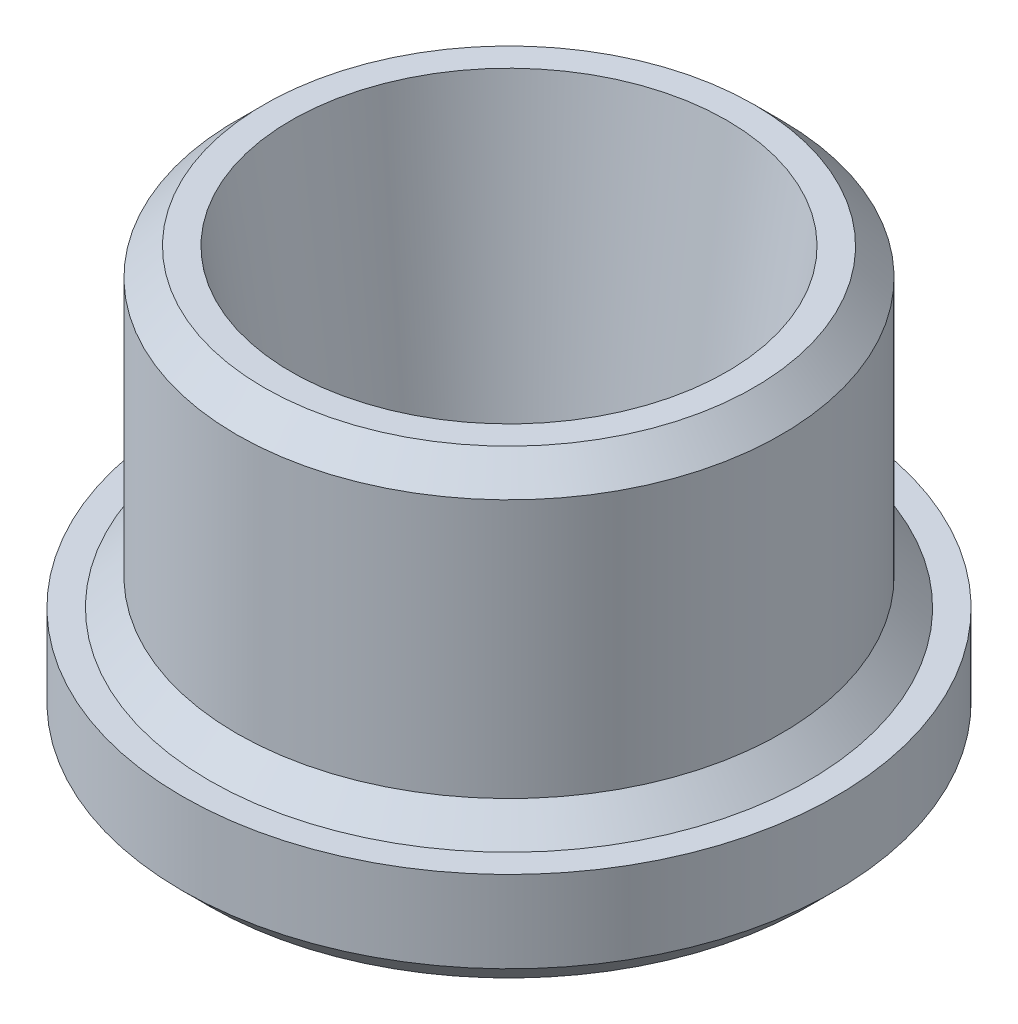
SolidWorks part; units mm, degrees
material "Alliage 1060"
ref_plane "Front Plane" through (0, 0, 0) normal (0, 0, 1) x (1, 0, 0)
ref_plane "Top Plane" through (0, 0, 0) normal (0, 1, 0) x (1, 0, 0)
ref_plane "Right Plane" through (0, 0, 0) normal (1, 0, 0) x (0, 0, -1)
sketch "Sketch1" plane through (0, 0, 0) normal (0, 0, 1) x (1, 0, 0)
  line L0 (0, -36.9603) -> (0, 51.414) construction
  line L1 (3.15, 0) -> (6, 0)
  line L2 (6, 0) -> (6, 2)
  line L3 (6, 2) -> (5.5, 2)
  line L4 (5, 2.5) -> (5, 7.75)
  line L5 (5, 7.75) -> (4, 7.75)
  line L6 (4, 7.75) -> (3.15, 1.75)
  line L7 (5.5, 2) -> (5, 2.5)
  line L8 (3.15, 1.75) -> (3.15, 0)
  dimension "D1" = 5
  dimension "D2" = 4
  dimension "D3" = 0.5
  dimension "D4" = 2
  dimension "D5" = 0.5
  dimension "D6" = 7.75
  dimension "D7" = 3.15
  dimension "D8" = 6
  dimension "D9" = 6
revolve "Revolve1" add sketch "Sketch1" angle 360 about L0
chamfer "Chanfrein1" distance 0.5 angle 45 1 edges at (0, 0, -6)
chamfer "Chanfrein2" distance 0.5 angle 45 1 edges at (0, 7.75, -5)
